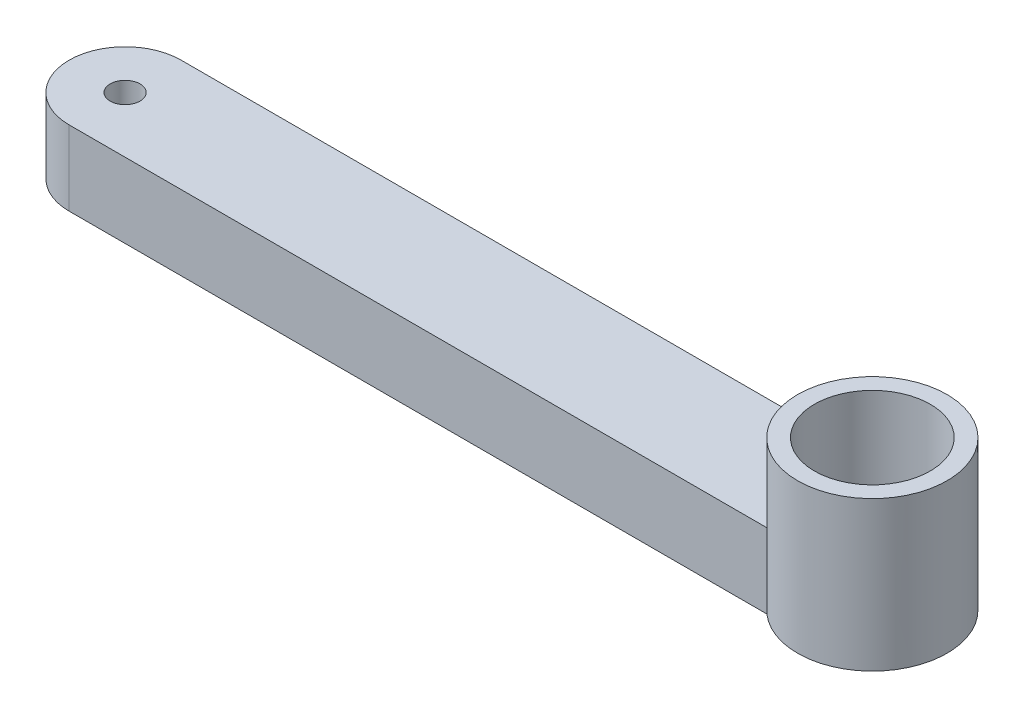
SolidWorks part; units mm, degrees
ref_plane "Front Plane" through (0, 0, 0) normal (0, 0, 1) x (1, 0, 0)
ref_plane "Top Plane" through (0, 0, 0) normal (0, 1, 0) x (1, 0, 0)
ref_plane "Right Plane" through (0, 0, 0) normal (1, 0, 0) x (0, 0, -1)
sketch "Sketch2" plane through (0, 0, 0) normal (0, 1, 0) x (1, 0, 0)
  line L0 (0, 0) -> (100, 0) construction
  line L1 (0, 7.5) -> (100, 7.5)
  line L2 (0, -7.5) -> (100, -7.5)
  arc A0 (0, 7.5) -> (0, -7.5) centre (0, 0) ccw
  arc A1 (100, -7.5) -> (100, 7.5) centre (100, 0) ccw
  circle A2 centre (0, 0) radius 2
  circle A3 centre (100, 0) radius 2.5
  point P3 (50, 0)
  dimension "D2" = 4
  dimension "D1" = 100
  dimension "D3" = 15
extrude "Boss-Extrude1" add sketch "Sketch2" along normal blind 10
sketch "Sketch3" plane through (0, 0, 0) normal (0, 1, 0) x (1, 0, 0)
  circle A0 centre (100, 0) radius 10
  dimension "D1" = 20
extrude "Boss-Extrude3" add sketch "Sketch3" along normal blind 20
sketch "Sketch4" plane through (0, 20, 0) normal (0, 1, 0) x (1, 0, 0)
  circle A0 centre (100, 0) radius 7.75
  dimension "D1" = 15.5
extrude "Cut-Extrude1" cut sketch "Sketch4" against normal up to next
